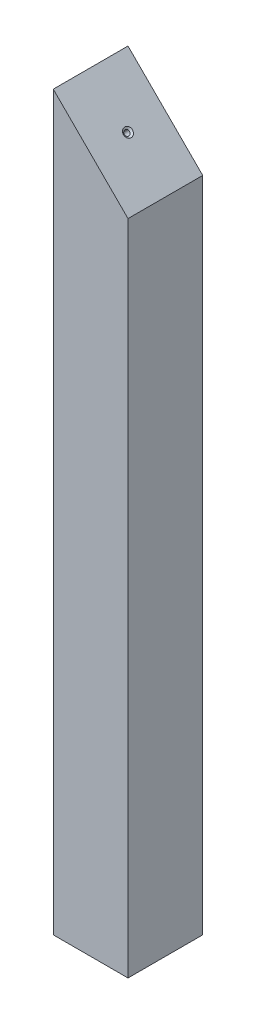
SolidWorks part; units mm, degrees
material "Balsa"
ref_plane "Front Plane" through (0, 0, 0) normal (0, 0, 1) x (1, 0, 0)
ref_plane "Top Plane" through (0, 0, 0) normal (0, 1, 0) x (1, 0, 0)
ref_plane "Right Plane" through (0, 0, 0) normal (1, 0, 0) x (0, 0, -1)
sketch "Sketch1" plane through (0, 0, 0) normal (0, 1, 0) x (1, 0, 0)
  line L1 (-12.7, 12.7) -> (12.7, 12.7)
  line L2 (-12.7, 12.7) -> (-12.7, -12.7)
  line L3 (-12.7, -12.7) -> (12.7, -12.7)
  line L4 (12.7, 12.7) -> (12.7, -12.7)
  line L5 (-12.7, 12.7) -> (12.7, -12.7) construction
  line L6 (-12.7, -12.7) -> (12.7, 12.7) construction
  point P0 (0, 0)
  dimension "D1" = 25.4
  dimension "D2" = 25.4
extrude "Boss-Extrude1" add sketch "Sketch1" along normal mid plane 248.97
hole_wizard "#0-80 Tapped Hole1" positions "Sketch2" profile "Sketch3" tap size "#0-80" standard "ANSI Inch"
sketch "Sketch2" plane through (0, -124.485, 0) normal (0, -1, 0) x (-1, 0, 0)
  point P0 (0, 0)
sketch "Sketch3" plane through (0, -124.485, 0) normal (1, 0, 0) x (0, 0, -1)
  line L0 (0, 0) -> (0, 20.3579)
  line L1 (0, 20.3579) -> (0.5956, 20)
  line L2 (0.5956, 20) -> (0.5956, 0.7683)
  line L3 (0.5956, 0.7683) -> (1.5113, 0)
  line L5 (1.5113, 0) -> (0, 0)
  line L6 (-0.5956, 0.7683) -> (-1.5113, 0) construction
  line L10 (0, 20.3579) -> (-0.5956, 20) construction
  line L11 (0, -6.35) -> (0, 107.95) construction
  dimension "Tap Drill Dia." = 1.1913
  dimension "Tap Drill Depth" = 20
  dimension "Near C'Sink Dia." = 3.0226
  dimension "Near C'Sink Angle" = 100
  dimension "Drill Angle" = 118
cosmetic thread "Hole Thread1" parameters "D1"=10, "D2"=1.524
sketch "Sketch4" plane through (0, 0, 0) normal (0, 0, 1) x (1, 0, 0)
  line L0 (12.7, 124.485) -> (-12.7, 124.485)
  line L1 (-12.7, 124.485) -> (12.7, 99.085)
  line L2 (12.7, 124.485) -> (12.7, -124.485) construction
  line L3 (12.7, 99.085) -> (12.7, 124.485)
  line L4 (-12.7, 124.485) -> (-12.7, -124.485) construction
  dimension "D1" = 45
extrude "Cut-Extrude1" cut sketch "Sketch4" against normal through all both and the other way through all
hole_wizard "CSK for #0 Flat Head Machine Screw (100)1" positions "Sketch5" profile "Sketch7" countersink size "#0" standard "ANSI Inch"
sketch "Sketch5" plane through (55.8925, 55.8925, 0) normal (0.7071, 0.7071, 0) x (0.7071, -0.7071, 0)
  line L0 (-97.0044, 12.7) -> (-61.0834, 12.7) construction
  line L1 (-97.0044, 12.7) -> (-97.0044, -12.7) construction
  point P0 (-79.0439, 0)
  point P4 (0, 0)
  point P7 (-79.0439, 12.7)
  point P8 (-79.0439, 5.2742)
  point P11 (-97.0044, 0)
sketch "Sketch7" plane through (0, 111.785, 0) normal (0, 0, 1) x (-0.7071, 0.7071, 0)
  line L0 (0, 0) -> (0, 10.5342)
  line L1 (0, 10.5342) -> (0.889, 10)
  line L2 (0.889, 10) -> (0.889, 0.5222)
  line L3 (0.889, 0.5222) -> (1.5113, 0)
  line L5 (1.5113, 0) -> (0, 0)
  line L6 (-0.889, 0.5222) -> (-1.5113, 0) construction
  line L10 (0, 10.5342) -> (-0.889, 10) construction
  line L11 (0, -6.35) -> (0, 107.95) construction
  dimension "Hole Dia." = 1.778
  dimension "Hole Depth" = 10
  dimension "Near C'Sink Dia." = 3.0226
  dimension "Near C'Sink Angle" = 100
  dimension "Drill Angle" = 118
